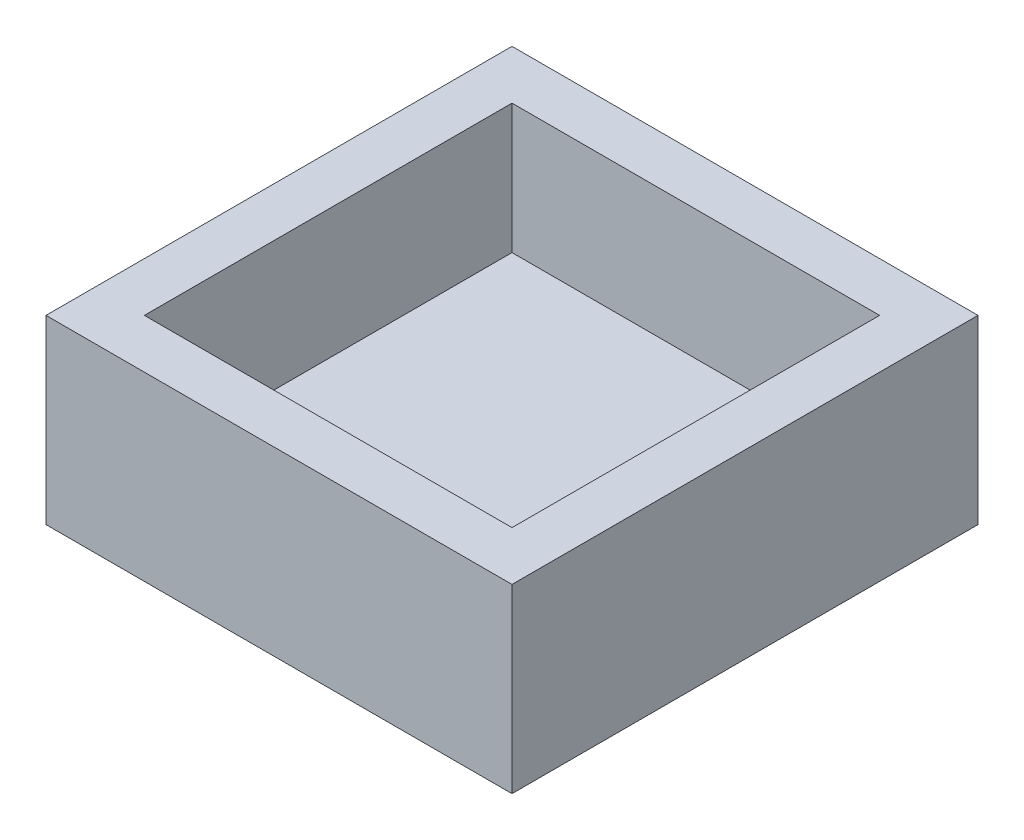
SolidWorks part; units mm, degrees
ref_plane "Front" through (0, 0, 0) normal (0, 0, 1) x (1, 0, 0)
ref_plane "Top" through (0, 0, 0) normal (0, 1, 0) x (1, 0, 0)
ref_plane "Right" through (0, 0, 0) normal (1, 0, 0) x (0, 0, -1)
sketch "Sketch1" plane through (0, 0, 0) normal (0, 1, 0) x (1, 0, 0)
  line L1 (-9, -9) -> (9, -9)
  line L2 (-9, -9) -> (-9, 9)
  line L3 (-9, 9) -> (9, 9)
  line L4 (9, -9) -> (9, 9)
  line L5 (-9, -9) -> (9, 9) construction
  line L6 (-9, 9) -> (9, -9) construction
  point P0 (0, 0)
  dimension "D1" = 18
extrude "Boss-Extrude1" add sketch "Sketch1" along normal blind 7
sketch "Sketch2" plane through (0, 7, 0) normal (0, 1, 0) x (1, 0, 0)
  line L1 (-7.1, 7.1) -> (7.1, 7.1)
  line L2 (-7.1, 7.1) -> (-7.1, -7.1)
  line L3 (-7.1, -7.1) -> (7.1, -7.1)
  line L4 (7.1, 7.1) -> (7.1, -7.1)
  line L5 (-7.1, 7.1) -> (7.1, -7.1) construction
  line L6 (-7.1, -7.1) -> (7.1, 7.1) construction
  point P0 (0, 0)
  dimension "D1" = 14.2
extrude "Cut-Extrude1" cut sketch "Sketch2" against normal blind 5
